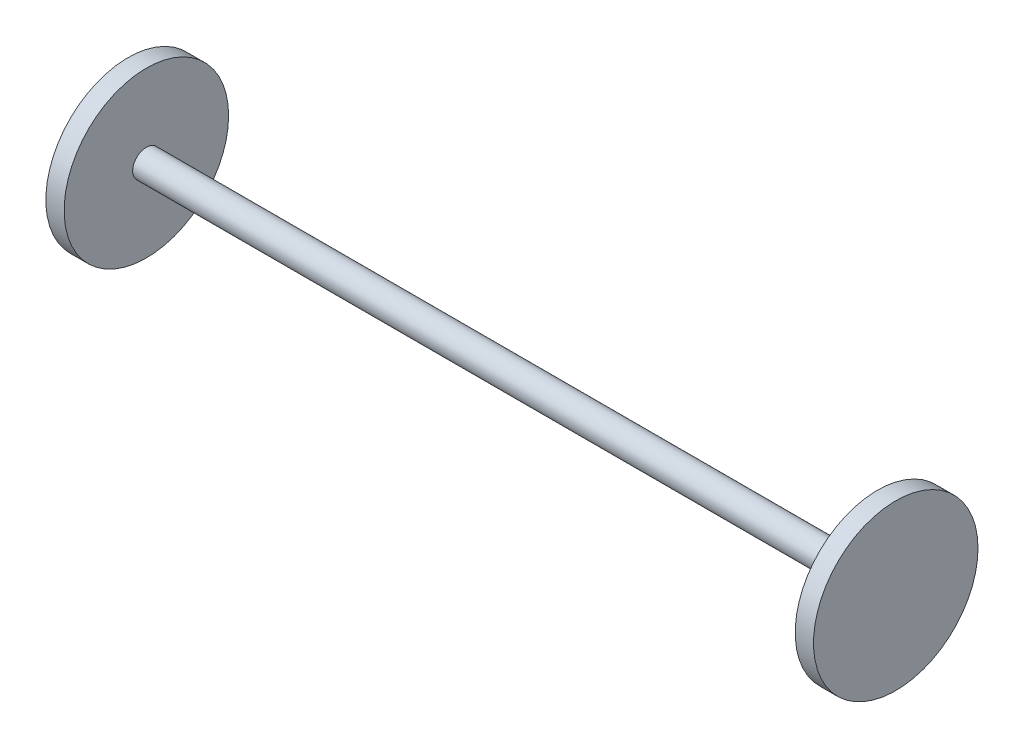
SolidWorks part; units mm, degrees
ref_plane "Front Plane" through (0, 0, 0) normal (0, 0, 1) x (1, 0, 0)
ref_plane "Top Plane" through (0, 0, 0) normal (0, 1, 0) x (1, 0, 0)
ref_plane "Right Plane" through (0, 0, 0) normal (1, 0, 0) x (0, 0, -1)
sketch "Sketch1" plane through (0, 0, 0) normal (1, 0, 0) x (0, 0, -1)
  circle A0 centre (0, 0) radius 7.5
  dimension "D1" = 15
extrude "Boss-Extrude1" add sketch "Sketch1" along normal mid plane 400
sketch "Sketch2" plane through (200, 0, 0) normal (1, 0, 0) x (0, 0, -1)
  circle A0 centre (0, 0) radius 45
  dimension "D1" = 90
extrude "Boss-Extrude2" add sketch "Sketch2" along normal blind 10
mirror "Mirror1" about plane through (0, 0, 0) normal (1, 0, 0) of "Boss-Extrude2"
